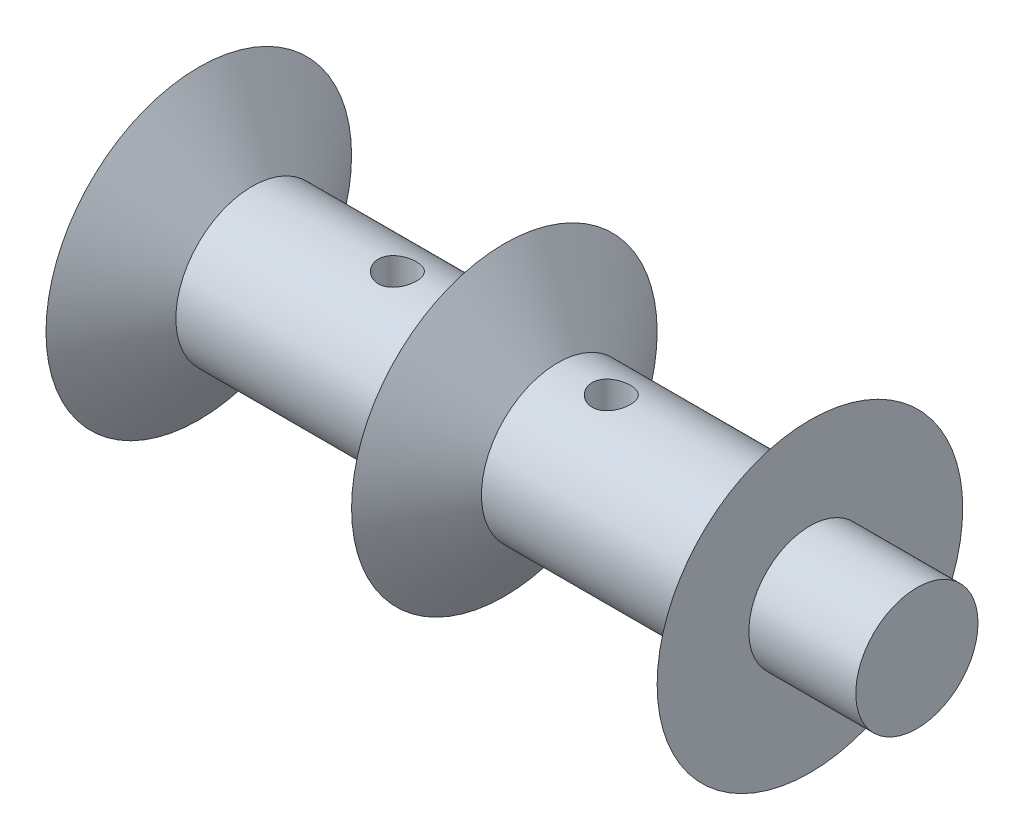
SolidWorks part; units mm, degrees
ref_plane "Front Plane" through (0, 0, 0) normal (0, 0, 1) x (1, 0, 0)
ref_plane "Top Plane" through (0, 0, 0) normal (0, 1, 0) x (1, 0, 0)
ref_plane "Right Plane" through (0, 0, 0) normal (1, 0, 0) x (0, 0, -1)
sketch "Sketch1" plane through (0, 0, 0) normal (0, 0, 1) x (1, 0, 0)
  line L0 (20, 0) -> (-20, 0)
  line L1 (-20, 10) -> (-20, 0)
  line L2 (16.5, 5) -> (20, 10)
  line L3 (-20, 10) -> (-16.5, 5)
  line L4 (-16.5, 5) -> (-3.5, 5)
  line L5 (-3.5, 5) -> (0, 10)
  line L6 (0, 0) -> (0, 1.6747) construction
  line L7 (20, 10) -> (20, 0)
  line L10 (16.5, 5) -> (3.5, 5)
  line L11 (3.5, 5) -> (0, 10)
  point P3 (0, 0)
  dimension "D1" = 40
  dimension "D2" = 5
  dimension "D3" = 3.5
  dimension "D4" = 3.5
  dimension "D5" = 13
  dimension "D6" = 10
  dimension "D7" = 5
revolve "Revolve1" add sketch "Sketch1" angle 360 about L0
sketch "Sketch2" plane through (-20, 0, 0) normal (-1, 0, 0) x (0, 0, 1)
  line L0 (-1.5, 2) -> (-1.5, -2)
  line L1 (0, 0) -> (0, -0.3908) construction
  line L2 (1.5, 2) -> (1.5, -2)
  circle A0 centre (0, 0) radius 2.5
  dimension "D1" = 5
  dimension "D2" = 3
extrude "Cut-Extrude1" cut sketch "Sketch2" against normal blind 9
sketch "Sketch3" plane through (-20, 0, 0) normal (-1, 0, 0) x (0, 0, 1)
  circle A0 centre (0, 0) radius 2.5
extrude "Cut-Extrude2" cut sketch "Sketch3" against normal blind 2.5
sketch "Sketch4" plane through (20, 0, 0) normal (1, 0, 0) x (0, 0, -1)
  circle A0 centre (0, 0) radius 4
extrude "Boss-Extrude1" add sketch "Sketch4" along normal blind 7
sketch "Sketch5" plane through (0, 0, 0) normal (0, 1, 0) x (1, 0, 0)
  line L0 (0, 0) -> (0, 6.0101) construction
  circle A0 centre (-7, 0) radius 1.25
  circle A1 centre (7, 0) radius 1.25
  dimension "D1" = 7
  dimension "D2" = 2.5
extrude "Cut-Extrude3" cut sketch "Sketch5" against normal through all and the other way through all
